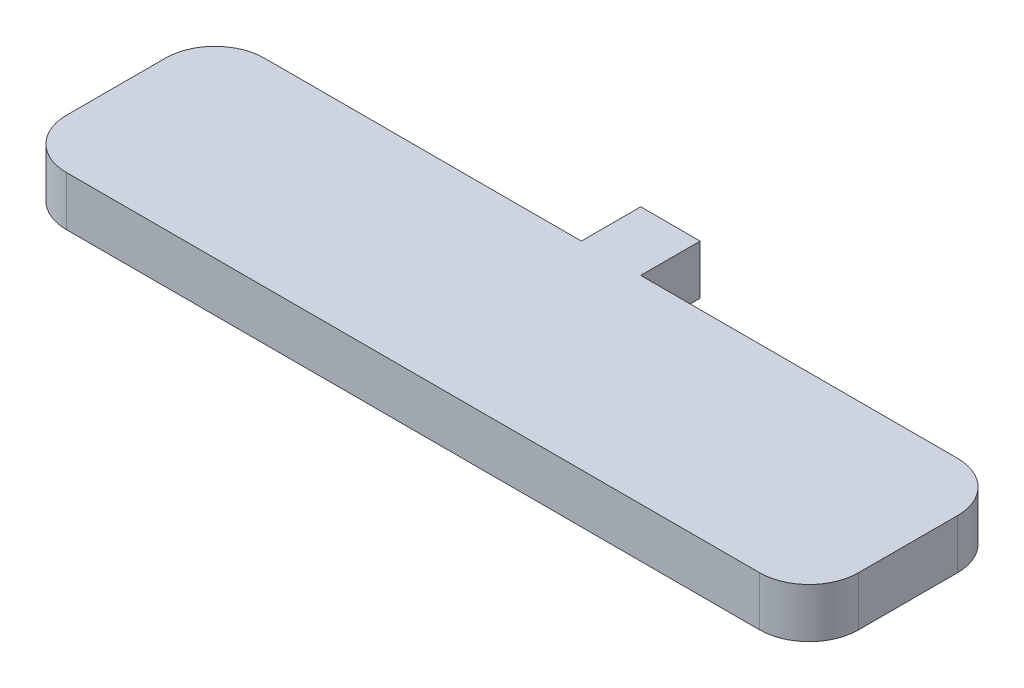
SolidWorks part; units mm, degrees
ref_plane "Front Plane" through (0, 0, 0) normal (0, 0, 1) x (1, 0, 0)
ref_plane "Top Plane" through (0, 0, 0) normal (0, 1, 0) x (1, 0, 0)
ref_plane "Right Plane" through (0, 0, 0) normal (1, 0, 0) x (0, 0, -1)
sketch "Sketch1" plane through (0, 0, 0) normal (0, 1, 0) x (1, 0, 0)
  line L1 (40, -10) -> (-40, -10)
  line L2 (40, -10) -> (40, 10)
  line L3 (40, 10) -> (-40, 10)
  line L4 (-40, -10) -> (-40, 10)
  line L5 (40, -10) -> (-40, 10) construction
  line L6 (40, 10) -> (-40, -10) construction
  point P0 (0, 0)
  dimension "D1" = 80
  dimension "D2" = 20
extrude "Boss-Extrude1" add sketch "Sketch1" along normal blind 5
fillet "Fillet1" radius 5 4 edges at (40, 2.5, 10) (40, 2.5, -10) (-40, 2.5, -10) (-40, 2.5, 10)
shell "Shell1" thickness 2
sketch "Sketch2" plane through (0, 0, -10) normal (0, 0, -1) x (-1, 0, 0)
  line L0 (0, -6.2057) -> (0, 17.696) construction
  line L1 (-35, 0) -> (35, 0) construction
  line L2 (3, 0) -> (-3, 0)
  line L3 (3, 0) -> (3, 5)
  line L4 (3, 5) -> (-3, 5)
  line L5 (-3, 0) -> (-3, 5)
  line L6 (-35, 5) -> (35, 5) construction
  dimension "D1" = 6
extrude "Boss-Extrude2" add sketch "Sketch2" along normal blind 6
sketch "Sketch3" plane through (0, 0, -16) normal (0, 0, -1) x (-1, 0, 0)
  line L3 (0, 0) -> (0, 6.9008) construction
  line L4 (-3, 0) -> (3, 0) construction
  circle A0 centre (0, 2.5) radius 1.425
  dimension "D1" = 2.85
  dimension "D2" = 2.5
extrude "Cut-Extrude2" cut sketch "Sketch3" against normal blind 4
